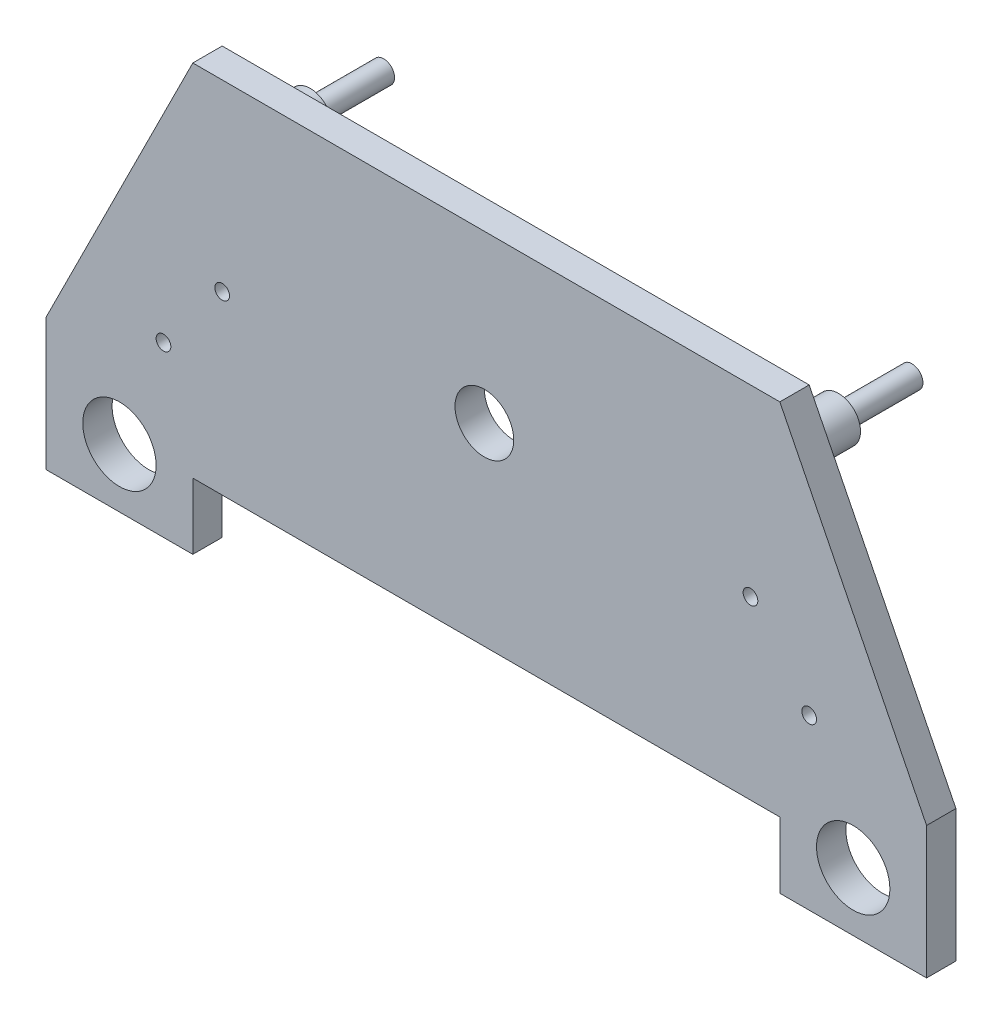
SolidWorks part; units mm, degrees
ref_plane "Front" through (0, 0, 0) normal (0, 0, 1) x (1, 0, 0)
ref_plane "Top" through (0, 0, 0) normal (0, 1, 0) x (1, 0, 0)
ref_plane "Right" through (0, 0, 0) normal (1, 0, 0) x (0, 0, -1)
sketch "草图1" plane through (0, 0, 0) normal (0, 0, 1) x (1, 0, 0)
  line L0 (-21.6856, 10.1426) -> (18.3144, 10.1426)
  line L1 (-21.6856, -9.8574) -> (18.3144, -9.8574)
  line L2 (-31.6856, -9.8574) -> (-31.6856, -18.8574)
  line L3 (-31.6856, -18.8574) -> (-21.6856, -18.8574)
  line L4 (-21.6856, -18.8574) -> (-21.6856, -9.8574)
  line L5 (28.3144, -9.8574) -> (28.3144, -18.8574)
  line L6 (28.3144, -18.8574) -> (18.3144, -18.8574)
  line L7 (18.3144, -18.8574) -> (18.3144, -9.8574)
  line L8 (-31.6856, -9.8574) -> (-21.6856, 10.1426)
  line L9 (28.3144, -9.8574) -> (18.3144, 10.1426)
  point P4 (-21.6856, 10.1426)
  point P11 (18.3144, 10.1426)
  dimension "D2" = 9
  dimension "D1" = 20
  dimension "D3" = 9
  dimension "D4" = 60
extrude "凸台-拉伸1" add sketch "草图1" along normal blind 2
sketch "草图2" plane through (0, 0, 0) normal (0, 0, 1) x (1, 0, 0)
  line L0 (-31.6856, -9.8574) -> (-31.6856, -18.8574) construction
  line L1 (-31.6856, -9.8574) -> (-31.6856, -18.8574) construction
  line L2 (-31.6856, -18.8574) -> (-21.6856, -18.8574) construction
  line L3 (18.3144, -9.8574) -> (18.3144, -18.8574) construction
  line L4 (18.3144, -9.8574) -> (18.3144, -18.8574) construction
  line L5 (-21.6856, -9.8574) -> (18.3144, -9.8574) construction
  line L6 (18.3144, -18.8574) -> (28.3144, -18.8574) construction
  line L7 (18.3144, -18.8574) -> (28.3144, -18.8574) construction
  circle A0 centre (-26.6856, -14.8574) radius 2.5
  circle A1 centre (23.3144, -14.8574) radius 2.5
  dimension "D1" = 5
  dimension "D5" = 5
  dimension "D6" = 5
  dimension "D2" = 4
  dimension "D3" = 5
  dimension "D4" = 4
extrude "切除-拉伸3" cut sketch "草图2" along normal through all
sketch "草图3" plane through (0, 0, 0) normal (0, 0, -1) x (-1, 0, 0)
  line L0 (-18.3144, 10.1426) -> (21.6856, 10.1426) construction
  line L1 (21.6856, -18.8574) -> (21.6856, -9.8574) construction
  line L2 (-18.3144, -9.8574) -> (-18.3144, -18.8574) construction
  circle A0 centre (-16.3144, 5.1426) radius 1.5
  circle A1 centre (19.6856, 5.1426) radius 1.5
  dimension "D1" = 3
  dimension "D2" = 3
  dimension "D3" = 5
  dimension "D4" = 5
  dimension "D5" = 2
  dimension "D6" = 2
extrude "凸台-拉伸2" add sketch "草图3" along normal blind 4
sketch "草图4" plane through (0, 0, -4) normal (0, 0, -1) x (-1, 0, 0)
  circle A0 centre (-16.3144, 5.1426) radius 0.75
  circle A1 centre (19.6856, 5.1426) radius 0.75
  dimension "D1" = 1.5
  dimension "D2" = 1.5
extrude "凸台-拉伸3" add sketch "草图4" along normal blind 5
sketch "草图5" plane through (0, 0, 0) normal (0, 0, 1) x (1, 0, 0)
  line L0 (-21.6856, -9.8574) -> (18.3144, -9.8574)
  line L1 (18.3144, -9.8574) -> (18.3144, -14.3574)
  line L2 (18.3144, -9.8574) -> (18.3144, -18.8574) construction
  line L3 (18.3144, -14.3574) -> (-21.6856, -14.3574)
  line L4 (-21.6856, -18.8574) -> (-21.6856, -9.8574) construction
  line L5 (-21.6856, -14.3574) -> (-21.6856, -9.8574)
extrude "凸台-拉伸4" add sketch "草图5" along normal blind 2
sketch "草图6" plane through (0, 0, 2) normal (0, 0, 1) x (1, 0, 0)
  line L0 (-31.6856, -9.8574) -> (-31.6856, -18.8574) construction
  line L1 (-21.6856, -14.3574) -> (18.3144, -14.3574) construction
  line L2 (28.3144, -18.8574) -> (28.3144, -9.8574) construction
  circle A0 centre (-23.6856, -7.3574) radius 0.5
  circle A1 centre (20.3144, -7.3574) radius 0.5
  circle A2 centre (-19.6856, -2.3574) radius 0.5
  circle A3 centre (16.3144, -2.3574) radius 0.5
  dimension "D1" = 8
  dimension "D5" = 1
  dimension "D6" = 1
  dimension "D2" = 7
  dimension "D3" = 8
  dimension "D4" = 7
  dimension "D7" = 12
  dimension "D8" = 12
  dimension "D9" = 12
  dimension "D10" = 12
extrude "切除-拉伸4" cut sketch "草图6" against normal blind 1
sketch "草图7" plane through (0, 0, 0) normal (0, 0, -1) x (-1, 0, 0)
  circle A0 centre (1.8181, -1.1811) radius 2
extrude "切除-拉伸5" cut sketch "草图7" against normal through all
